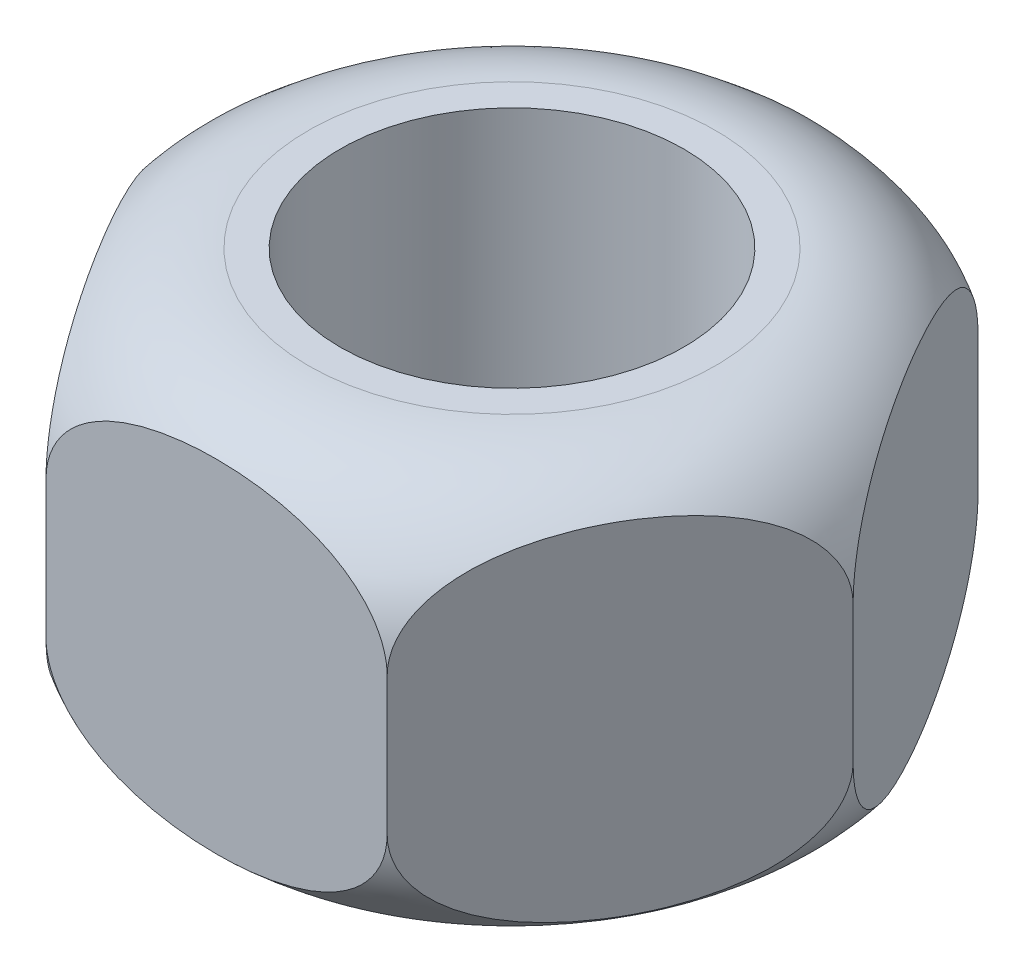
SolidWorks part; units mm, degrees
ref_plane "Front Plane" through (0, 0, 0) normal (0, 0, 1) x (1, 0, 0)
ref_plane "Top Plane" through (0, 0, 0) normal (0, 1, 0) x (1, 0, 0)
ref_plane "Right Plane" through (0, 0, 0) normal (1, 0, 0) x (0, 0, -1)
sketch "Sketch2" plane through (0, 0, 0) normal (0, 1, 0) x (1, 0, 0)
  line L1 (2.4826, 0) -> (1.2413, 2.15)
  line L2 (1.2413, 2.15) -> (-1.2413, 2.15)
  line L3 (-1.2413, 2.15) -> (-2.4826, 0)
  line L4 (-2.4826, 0) -> (-1.2413, -2.15)
  line L5 (-1.2413, -2.15) -> (1.2413, -2.15)
  line L6 (1.2413, -2.15) -> (2.4826, 0)
  circle A0 centre (0, 0) radius 2.15 construction
  circle A1 centre (0, 0) radius 1.25
  dimension "D2" = 2.5
  dimension "D1" = 4.3
extrude "Boss-Extrude1" add sketch "Sketch2" along normal blind 3
sketch "Sketch3" plane through (0, 0, 0) normal (0, 0, 1) x (1, 0, 0)
  line L0 (1.2413, 0) -> (2.4826, 0) construction
  line L2 (1.2413, 3) -> (2.4826, 3) construction
  line L3 (2.4826, 0) -> (1.4826, 0)
  line L5 (2.4826, 3) -> (1.4826, 3)
  line L6 (0, 0) -> (0, -0.3473) construction
  line L7 (2.4826, 3) -> (2.4826, 2)
  line L8 (2.4826, 0) -> (2.4826, 1)
  arc A0 (1.4826, 0) -> (2.4826, 1) centre (1.4826, 1) ccw
  arc A1 (2.4826, 2) -> (1.4826, 3) centre (1.4826, 2) ccw
  dimension "D1" = 1
revolve "Cut-Revolve1" cut sketch "Sketch3" angle 360 about L6
